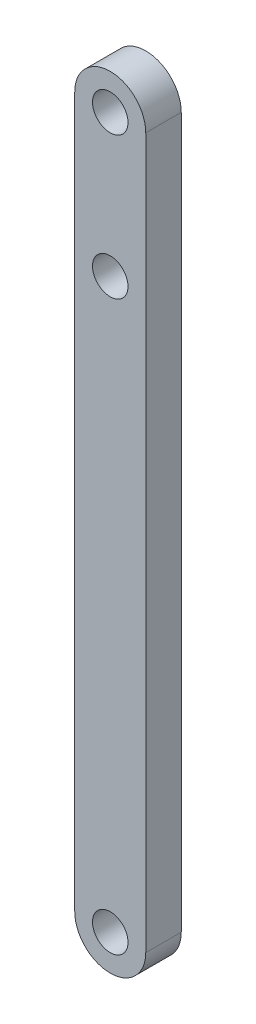
SolidWorks part; units mm, degrees
material "7075-O (SS)"
ref_plane "前视基准面" through (0, 0, 0) normal (0, 0, 1) x (1, 0, 0)
ref_plane "上视基准面" through (0, 0, 0) normal (0, 1, 0) x (1, 0, 0)
ref_plane "右视基准面" through (0, 0, 0) normal (1, 0, 0) x (0, 0, -1)
sketch "草图1" plane through (0, 0, 0) normal (0, 0, 1) x (1, 0, 0)
  line L0 (0, 0) -> (0, 60)
  line L2 (6, 60) -> (6, 0)
  arc A0 (6, 60) -> (0, 60) centre (3, 60) ccw
  arc A1 (0, 0) -> (6, 0) centre (3, 0) ccw
extrude "凸台-拉伸1" add sketch "草图1" along normal blind 3
sketch "草图3" plane through (0, 0, 0) normal (0, 0, 1) x (1, 0, 0)
  line L0 (3, 60) -> (3, 48) construction
  circle A0 centre (3, 0) radius 1.5
  circle A1 centre (3, 60) radius 1.5
  circle A2 centre (3, 48) radius 1.5
extrude "切除-拉伸3" cut sketch "草图3" along normal blind 5
